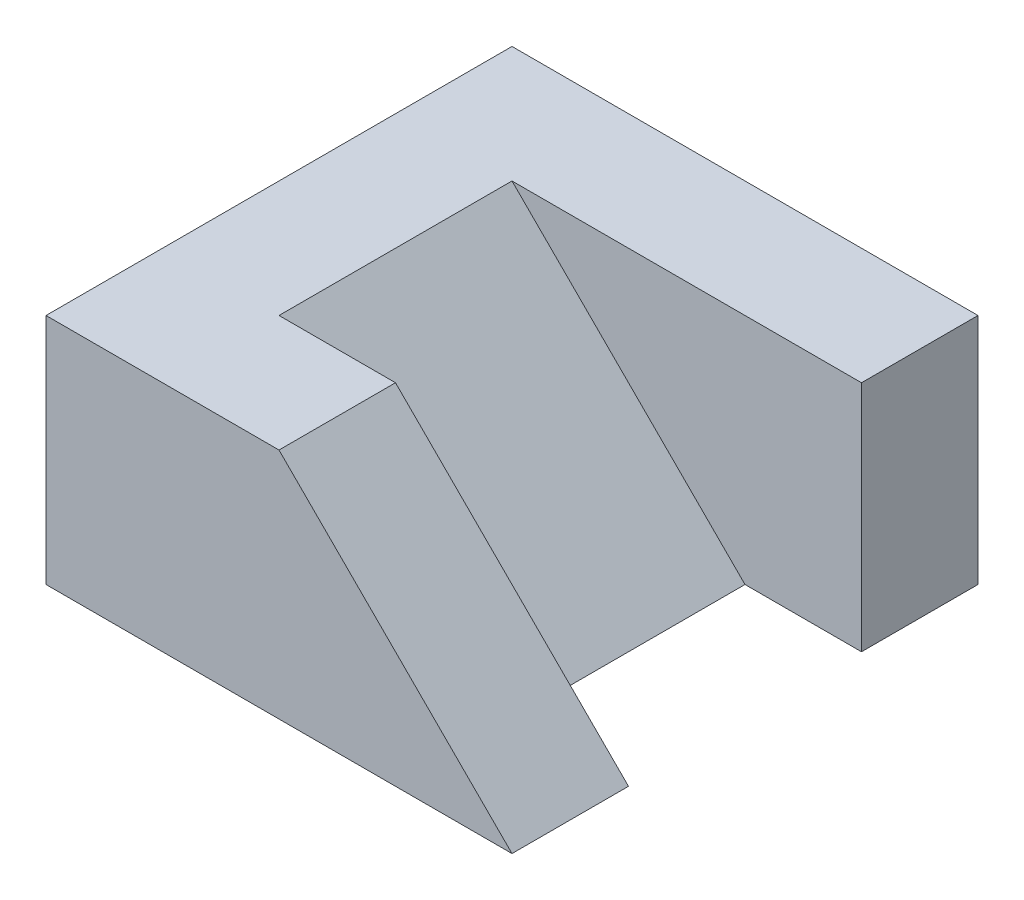
SolidWorks part; units mm, degrees
ref_plane "前基準面" through (0, 0, 0) normal (0, 0, 1) x (1, 0, 0)
ref_plane "上基準面" through (0, 0, 0) normal (0, 1, 0) x (1, 0, 0)
ref_plane "右基準面" through (0, 0, 0) normal (1, 0, 0) x (0, 0, -1)
sketch "草圖1" plane through (0, 0, 0) normal (0, 1, 0) x (1, 0, 0)
  line L1 (10, 10) -> (-10, 10)
  line L2 (10, 10) -> (10, -10)
  line L3 (10, -10) -> (-10, -10)
  line L4 (-10, 10) -> (-10, -10)
  line L5 (10, 10) -> (-10, -10) construction
  line L6 (10, -10) -> (-10, 10) construction
  line L7 (10, 5) -> (5, 5)
  line L8 (10, 5) -> (10, -5)
  line L9 (10, -5) -> (5, -5)
  line L10 (5, 5) -> (5, -5)
  point P0 (0, 0)
  dimension "D1" = 20
  dimension "D2" = 20
  dimension "D3" = 5
  dimension "D4" = 5
  dimension "D5" = 10
extrude "填料-伸長1" add sketch "草圖1" along normal blind 10 contours L10 L7 L2 L1 L4 L3 L9
sketch "草圖2" plane through (0, 0, 10) normal (0, 0, 1) x (1, 0, 0)
  line L1 (10, 10) -> (-10, 10) construction
  line L2 (10, 10) -> (10, 0) construction
  line L3 (10, 0) -> (10, 10)
  line L4 (10, 10) -> (-5, 10)
  line L5 (-5, 10) -> (5, 0)
  line L6 (10, 0) -> (-10, 0) construction
  line L7 (5, 0) -> (10, 0)
  dimension "D1" = 5
  dimension "D2" = 5
extrude "除料-伸長1" cut sketch "草圖2" against normal blind 10 from offset 5 offset against normal yes
sketch "草圖3" plane through (0, 0, 10) normal (0, 0, 1) x (1, 0, 0)
  line L0 (0, 10) -> (10, 0)
  line L1 (10, 10) -> (-10, 10) construction
  line L2 (10, 0) -> (10, 10)
  line L3 (10, 10) -> (0, 10)
  dimension "D1" = 10
extrude "除料-伸長2" cut sketch "草圖3" against normal blind 5
